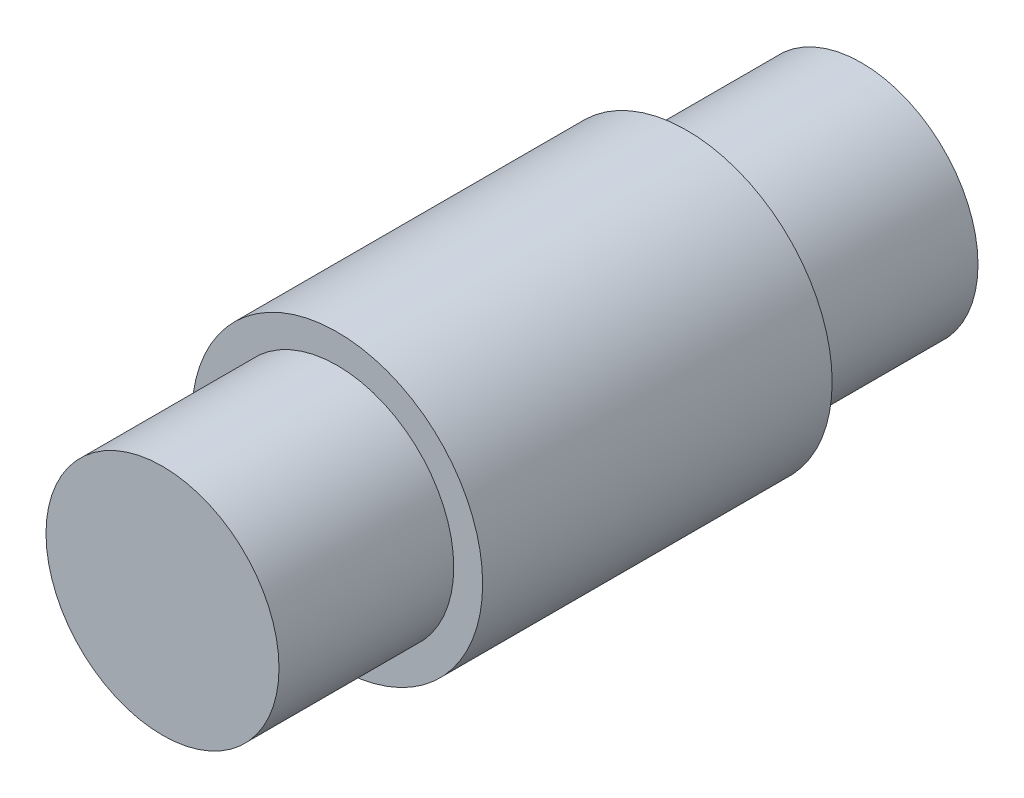
SolidWorks part; units mm, degrees
ref_plane "Front Plane" through (0, 0, 0) normal (0, 0, 1) x (1, 0, 0)
ref_plane "Top Plane" through (0, 0, 0) normal (0, 1, 0) x (1, 0, 0)
ref_plane "Right Plane" through (0, 0, 0) normal (1, 0, 0) x (0, 0, -1)
sketch "Sketch1" plane through (0, 0, 0) normal (0, 0, 1) x (1, 0, 0)
  circle A0 centre (0, 0) radius 3.9624
  dimension "D1" = 7.9248
extrude "Boss-Extrude1" add sketch "Sketch1" along normal mid plane 9.525
sketch "Sketch2" plane through (0, 0, 0) normal (0, 0, 1) x (1, 0, 0)
  circle A0 centre (0, 0) radius 3.175
  dimension "D1" = 6.35
extrude "Boss-Extrude2" add sketch "Sketch2" along normal mid plane 19.05
